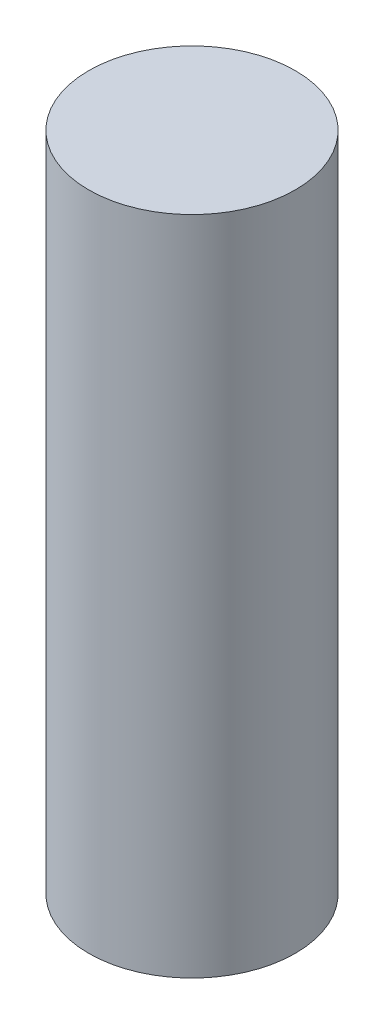
SolidWorks part; units mm, degrees
ref_plane "Front Plane" through (0, 0, 0) normal (0, 0, 1) x (1, 0, 0)
ref_plane "Top Plane" through (0, 0, 0) normal (0, 1, 0) x (1, 0, 0)
ref_plane "Right Plane" through (0, 0, 0) normal (1, 0, 0) x (0, 0, -1)
sketch "Sketch1" plane through (0, 0, 0) normal (0, 1, 0) x (1, 0, 0)
  circle A0 centre (0, 0) radius 0.3125
  dimension "D1" = 0.625
extrude "Boss-Extrude1" add sketch "Sketch1" along normal mid plane 2
